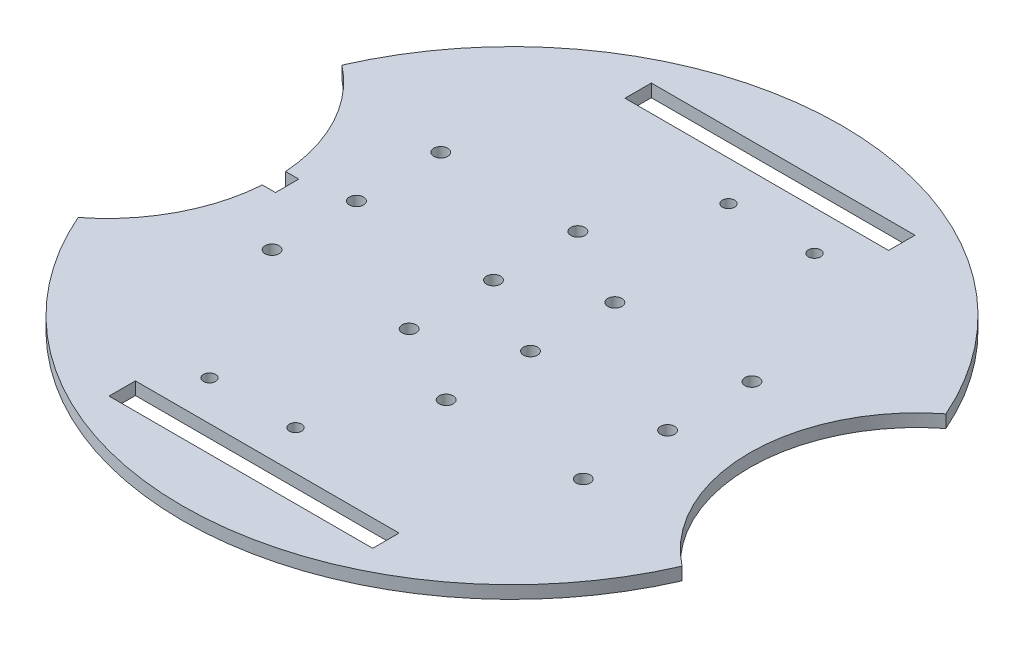
SolidWorks part; units mm, degrees
ref_plane "Front" through (0, 0, 0) normal (0, 0, 1) x (1, 0, 0)
ref_plane "Top" through (0, 0, 0) normal (0, 1, 0) x (1, 0, 0)
ref_plane "Right" through (0, 0, 0) normal (1, 0, 0) x (0, 0, -1)
sketch "Sketch1" plane through (0, 0, 0) normal (0, 1, 0) x (1, 0, 0)
  circle A0 centre (0, 0) radius 75
  dimension "D1" = 150
extrude "Boss-Extrude1" add sketch "Sketch1" along normal blind 2.9
sketch "Sketch2" plane through (0, 2.9, 0) normal (0, 1, 0) x (1, 0, 0)
  line L0 (-24.7, 25.6) -> (-24.7, -25.6) construction
  line L1 (-43.5, 28.4908) -> (-5.9, 28.4908) construction
  line L2 (-43.5, 28.4908) -> (-43.5, -22.7092) construction
  line L3 (-43.5, -22.7092) -> (-5.9, -22.7092) construction
  line L4 (-5.9, 28.4908) -> (-5.9, -22.7092) construction
  line L5 (-27.7, -22.7092) -> (-21.7, -22.7092) construction
  line L6 (-27.7, -22.7092) -> (-27.7, -42.7092) construction
  line L7 (-27.7, -42.7092) -> (-21.7, -42.7092)
  line L8 (-21.7, -22.7092) -> (-21.7, -42.7092) construction
  line L9 (24.7, 25.6) -> (24.7, -25.6) construction
  line L10 (5.9, 22.7092) -> (43.5, 22.7092) construction
  line L11 (5.9, 22.7092) -> (5.9, -28.4908) construction
  line L12 (5.9, -28.4908) -> (43.5, -28.4908) construction
  line L13 (43.5, 22.7092) -> (43.5, -28.4908) construction
  line L14 (0, 75) -> (0, -75) construction
  line L15 (21.7, 22.7092) -> (27.7, 22.7092) construction
  line L16 (21.7, 22.7092) -> (21.7, 42.7092) construction
  line L17 (21.7, 42.7092) -> (27.7, 42.7092)
  line L18 (27.7, 22.7092) -> (27.7, 42.7092) construction
  line L19 (-75, 0) -> (75, 0) construction
  line L20 (-54.0852, 0) -> (-54.0852, -59.9004) construction
  line L21 (-37.05, -42.7092) -> (-12.35, -42.7092) construction
  line L22 (-37.05, -42.7092) -> (-37.05, -52.7092) construction
  line L23 (-37.05, -52.7092) -> (-12.35, -52.7092) construction
  line L24 (-12.35, -42.7092) -> (-12.35, -52.7092) construction
  line L25 (12.35, 42.7092) -> (37.05, 42.7092) construction
  line L26 (12.35, 42.7092) -> (12.35, 52.7092) construction
  line L27 (12.35, 52.7092) -> (37.05, 52.7092) construction
  line L28 (37.05, 42.7092) -> (37.05, 52.7092) construction
  line L29 (-68.7285, 30.0232) -> (-92.1852, 0) construction
  line L30 (-68.7285, -30.0232) -> (-92.1852, 0) construction
  line L31 (-75, 0) -> (-75, -48.0416) construction
  line L32 (74.91, 3.6727) -> (70.3716, 3.6727) construction
  line L33 (70.3716, 3.6727) -> (70.3716, -3.6727) construction
  line L34 (70.3716, -3.6727) -> (74.91, -3.6727) construction
  line L35 (40.6357, -63.0376) -> (38.3665, -59.1072) construction
  line L36 (38.3665, -59.1072) -> (32.0051, -62.7799) construction
  line L37 (32.0051, -62.7799) -> (34.2744, -66.7103) construction
  line L38 (-34.2744, -66.7103) -> (-32.0051, -62.7799) construction
  line L39 (-32.0051, -62.7799) -> (-38.3665, -59.1072) construction
  line L40 (-38.3665, -59.1072) -> (-40.6357, -63.0376) construction
  line L41 (-74.91, -3.6727) -> (-70.3716, -3.6727) construction
  line L42 (-70.3716, -3.6727) -> (-70.3716, 3.6727) construction
  line L43 (-70.3716, 3.6727) -> (-74.91, 3.6727) construction
  line L44 (-40.6357, 63.0376) -> (-38.3665, 59.1072) construction
  line L45 (-38.3665, 59.1072) -> (-32.0051, 62.7799) construction
  line L46 (-32.0051, 62.7799) -> (-34.2744, 66.7103) construction
  line L47 (34.2744, 66.7103) -> (32.0051, 62.7799) construction
  line L48 (32.0051, 62.7799) -> (38.3665, 59.1072) construction
  line L49 (38.3665, 59.1072) -> (40.6357, 63.0376) construction
  line L51 (-30, -55.7092) -> (30, -55.7092)
  line L52 (-30, -55.7092) -> (-30, -61.7092)
  line L53 (-30, -61.7092) -> (30, -61.7092)
  line L54 (30, -55.7092) -> (30, -61.7092)
  line L55 (-30, 61.7092) -> (30, 61.7092)
  line L56 (-30, 61.7092) -> (-30, 55.7092)
  line L57 (-30, 55.7092) -> (30, 55.7092)
  line L58 (30, 61.7092) -> (30, 55.7092)
  circle A0 centre (0, 0) radius 75 construction
  circle A1 centre (-92.1852, 0) radius 38.1 construction
  arc A2 (-68.7285, 30.0232) -> (-68.7285, -30.0232) centre (-92.1852, 0) cw
  arc A3 (68.7285, 30.0232) -> (68.7285, -30.0232) centre (92.1852, 0) ccw
  circle A4 centre (-40.3, -14.3092) radius 1.6
  circle A5 centre (-40.3, 4.8908) radius 1.6
  circle A6 centre (-40.3, 24.0908) radius 1.6
  circle A7 centre (-9.1, -14.3092) radius 1.6
  circle A8 centre (-9.1, 4.8908) radius 1.6
  circle A9 centre (-9.1, 24.0908) radius 1.6
  circle A10 centre (40.3, 14.3092) radius 1.6
  circle A11 centre (40.3, -4.8908) radius 1.6
  circle A12 centre (40.3, -24.0908) radius 1.6
  circle A13 centre (9.1, -24.0908) radius 1.6
  circle A14 centre (9.1, -4.8908) radius 1.6
  circle A15 centre (9.1, 14.3092) radius 1.6
  circle A16 centre (-22.14, -46.7092) radius 1.4
  circle A17 centre (-22.14, -46.7092) radius 2.56 construction
  circle A18 centre (-2.56, -46.7092) radius 1.4
  circle A19 centre (-2.56, -46.7092) radius 2.56 construction
  circle A20 centre (22.14, 46.7092) radius 1.4
  circle A21 centre (22.14, 46.7092) radius 2.56 construction
  circle A22 centre (2.56, 46.7092) radius 1.4
  circle A23 centre (2.56, 46.7092) radius 2.56 construction
  point P39 (-68.7285, 30.0232)
  point P40 (-68.7285, -30.0232)
  point P74 (0, 0)
  circle M2 centre (0, 0) radius 75
  dimension "D10" = 76.2
  dimension "D16" = 6
  dimension "D17" = 3
  dimension "D18" = 19.2
  dimension "D19" = 3
  dimension "D20" = 31.2
  dimension "D21" = 3.2
  dimension "D22" = 3.2
  dimension "D24" = 8.4
  dimension "D25" = 31.2
  dimension "D26" = 2.8
  dimension "D27" = 5.12
  dimension "D28" = 4
  dimension "D29" = 5.12
  dimension "D30" = 2.8
  dimension "D31" = 5.12
  dimension "D32" = 2.8
  dimension "D34" = 5.12
  dimension "D35" = 2.8
  dimension "D1" = 37.6
  dimension "D2" = 51.2
  dimension "D3" = 6
  dimension "D4" = 20
  dimension "D5" = 37.6
  dimension "D6" = 51.2
  dimension "D7" = 6
  dimension "D8" = 20
  dimension "D9" = 24.7
  dimension "D11" = 10
  dimension "D12" = 24.7
  dimension "D13" = 10
  dimension "D14" = 24.7
  dimension "D15" = 104
  dimension "D33" = 4
  dimension "D36" = 11.8
  dimension "D37" = 60
  dimension "D38" = 6
  dimension "D39" = 60
  dimension "D40" = 6
  dimension "D41" = 3
  dimension "D42" = 8.4
  dimension "D23" = 3
extrude "Cut-Extrude1" cut sketch "Sketch2" against normal blind 10 contours A2 M2 | A3 M2 | A13 | A12 | A11 | A10 | A15 | A14 | A8 | A7 | A9 | A6 | A5 | A4 | A16 | A18 | A20 | A22 | L54 L51 L52 L53 | L58 L55 L56 L57
sketch "Sketch3" plane through (0, 2.9, 0) normal (0, 1, 0) x (1, 0, 0)
  line L0 (-54.0852, 0) -> (54.0852, 0) construction
  line L1 (-54.1775, 2.65) -> (-51.1775, 2.65)
  line L2 (-51.1775, 2.65) -> (-51.1775, -2.65)
  line L3 (-51.1775, -2.65) -> (-54.1775, -2.65)
  arc A0 (-68.7285, -30.0232) -> (-68.7285, 30.0232) centre (-92.1852, 0) ccw construction
  arc A1 (68.7285, 30.0232) -> (68.7285, -30.0232) centre (92.1852, 0) ccw construction
  arc M17 (-68.7285, 30.0232) -> (-68.7285, -30.0232) centre (-92.1852, 0) cw
  dimension "D1" = 3
  dimension "D2" = 5.3
extrude "Cut-Extrude2" cut sketch "Sketch3" against normal through all contours L0 L2 L1 M17 | L0 L3 L2 M17
